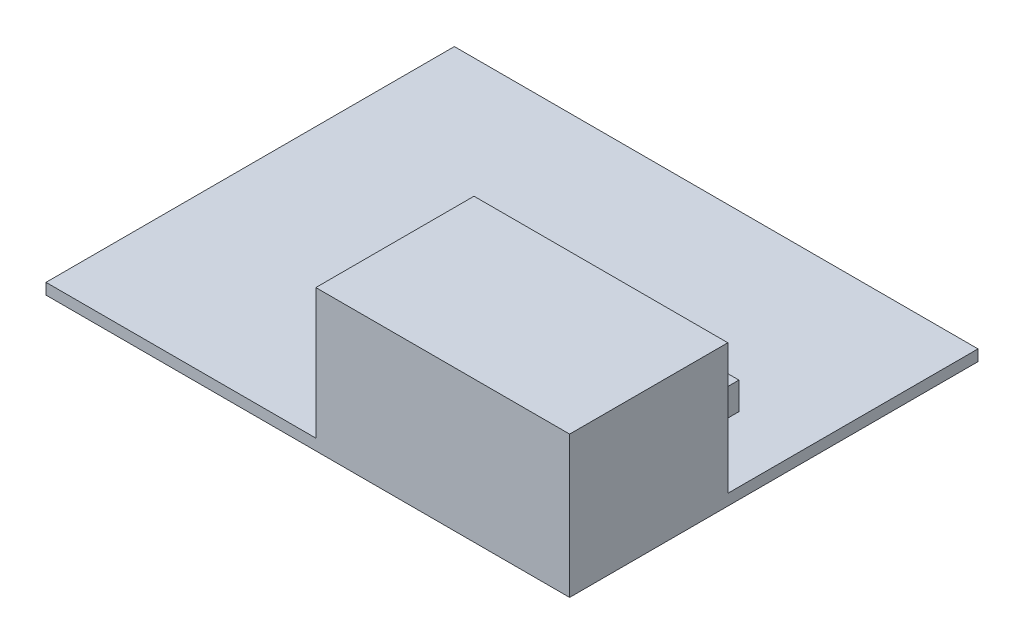
SolidWorks part; units mm, degrees
ref_plane "Front Plane" through (0, 0, 0) normal (0, 0, 1) x (1, 0, 0)
ref_plane "Top Plane" through (0, 0, 0) normal (0, 1, 0) x (1, 0, 0)
ref_plane "Right Plane" through (0, 0, 0) normal (1, 0, 0) x (0, 0, -1)
sketch "Sketch1" plane through (0, 0, 0) normal (0, 1, 0) x (1, 0, 0)
  line L1 (38.2524, -29.8323) -> (-38.2524, -29.8323)
  line L2 (38.2524, -29.8323) -> (38.2524, 29.8323)
  line L3 (38.2524, 29.8323) -> (-38.2524, 29.8323)
  line L4 (-38.2524, -29.8323) -> (-38.2524, 29.8323)
  line L5 (38.2524, -29.8323) -> (-38.2524, 29.8323) construction
  line L6 (38.2524, 29.8323) -> (-38.2524, -29.8323) construction
  point P0 (0, 0)
  dimension "D1" = 76.5048
  dimension "D2" = 59.6646
extrude "Boss-Extrude1" add sketch "Sketch1" along normal blind 1.62
sketch "Sketch2" plane through (0, 1.62, 0) normal (0, 1, 0) x (1, 0, 0)
  line L1 (38.2524, -29.8323) -> (1.1684, -29.8323)
  line L2 (38.2524, -29.8323) -> (38.2524, -6.7183)
  line L3 (38.2524, -6.7183) -> (1.1684, -6.7183)
  line L4 (1.1684, -29.8323) -> (1.1684, -6.7183)
  dimension "D1" = 37.084
  dimension "D2" = 23.114
extrude "Boss-Extrude2" add sketch "Sketch2" along normal blind 19.05
sketch "Sketch3" plane through (0, 1.62, 0) normal (0, 1, 0) x (1, 0, 0)
  line L0 (38.2524, -6.7183) -> (38.2524, 29.8323) construction
  line L1 (28.7338, -0.5829) -> (22.371, -0.5829)
  line L2 (28.7338, -0.5829) -> (28.7338, 4.4183)
  line L3 (28.7338, 4.4183) -> (22.371, 4.4183)
  line L4 (22.371, -0.5829) -> (22.371, 4.4183)
  line L5 (28.7338, -0.5829) -> (22.371, 4.4183) construction
  line L6 (28.7338, 4.4183) -> (22.371, -0.5829) construction
  line L7 (-38.2524, -29.8323) -> (1.1684, -29.8323) construction
  point P0 (25.5524, 1.9177)
  point P9 (25.5524, 2.2466)
  dimension "D1" = 12.7
  dimension "D2" = 31.75
extrude "Boss-Extrude3" add sketch "Sketch3" along normal blind 4
